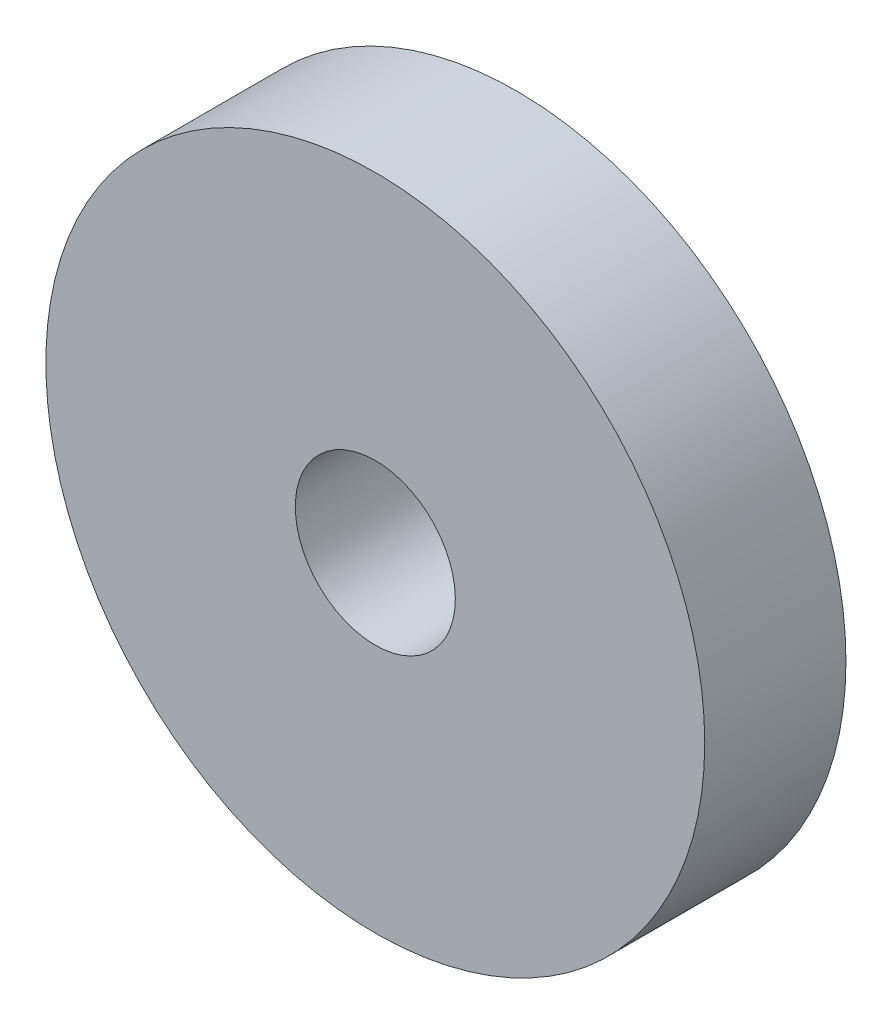
SolidWorks part; units mm, degrees
ref_plane "Front Plane" through (0, 0, 0) normal (0, 0, 1) x (1, 0, 0)
ref_plane "Top Plane" through (0, 0, 0) normal (0, 1, 0) x (1, 0, 0)
ref_plane "Right Plane" through (0, 0, 0) normal (1, 0, 0) x (0, 0, -1)
sketch "Sketch1" plane through (0, 0, 0) normal (0, 0, 1) x (1, 0, 0)
  circle A1 centre (0, 0) radius 7
extrude "Boss-Extrude1" add sketch "Sketch1" along normal blind 3
sketch "Sketch2" plane through (0, 0, 3) normal (0, 0, 1) x (1, 0, 0)
  circle A0 centre (0, 0) radius 1.7
extrude "Cut-Extrude1" cut sketch "Sketch2" against normal up to surface (3 mm away) up to face at (7, 0, 0)
